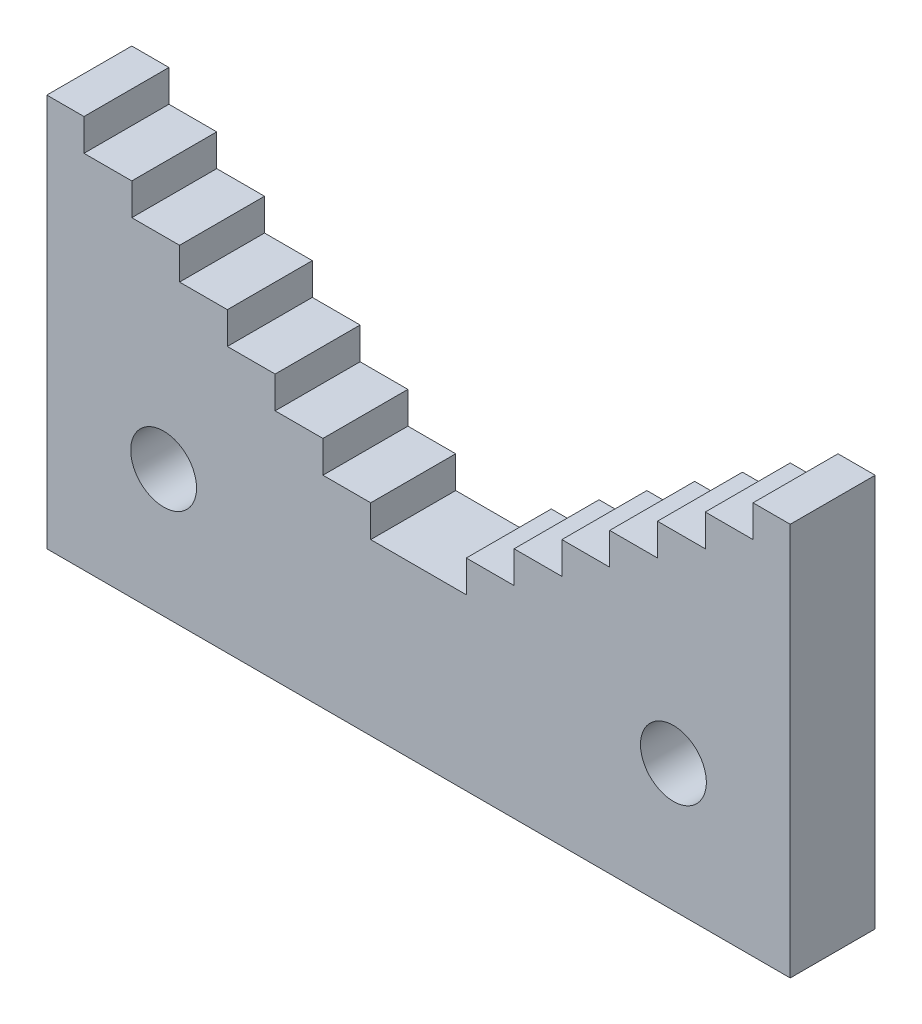
SolidWorks part; units mm, degrees
ref_plane "Front Plane" through (0, 0, 0) normal (0, 0, 1) x (1, 0, 0)
ref_plane "Top Plane" through (0, 0, 0) normal (0, 1, 0) x (1, 0, 0)
ref_plane "Right Plane" through (0, 0, 0) normal (1, 0, 0) x (0, 0, -1)
sketch "Sketch1" plane through (0, 0, 0) normal (0, 0, 1) x (1, 0, 0)
  line L0 (35, 0) -> (-35, 0) construction
  line L1 (-35, 0) -> (-35, 37)
  line L2 (-35, 37) -> (-31.5, 37)
  line L3 (-31.5, 37) -> (-31.5, 34)
  line L4 (-31.5, 34) -> (-27, 34)
  line L5 (-27, 34) -> (-27, 31)
  line L6 (-27, 31) -> (-22.5, 31)
  line L7 (-22.5, 31) -> (-22.5, 28)
  line L8 (-22.5, 28) -> (-18, 28)
  line L9 (-18, 28) -> (-18, 25)
  line L10 (-18, 25) -> (-13.5, 25)
  line L11 (-13.5, 25) -> (-13.5, 22)
  line L12 (-13.5, 22) -> (-9, 22)
  line L13 (-9, 22) -> (-9, 19)
  line L14 (-9, 19) -> (-4.5, 19)
  line L15 (-4.5, 19) -> (-4.5, 16)
  line L16 (-4.5, 16) -> (0, 16)
  line L17 (0, 16) -> (0, 0)
  line L18 (0, 0) -> (-35, 0)
  line L19 (0, 16) -> (0, 35.4494) construction
  circle A0 centre (-24, 12) radius 3.1
  point P4 (0, 0)
  dimension "D6" = 6.2
  dimension "D1" = 70
  dimension "D2" = 4.5
  dimension "D3" = 3.5
  dimension "D4" = 3
  dimension "D5" = 37
  dimension "D7" = 12
  dimension "D8" = 24
extrude "Boss-Extrude1" add sketch "Sketch1" along normal blind 8
mirror "Mirror1" about plane through (0, 0, 0) normal (1, 0, 0) of "Boss-Extrude1"
